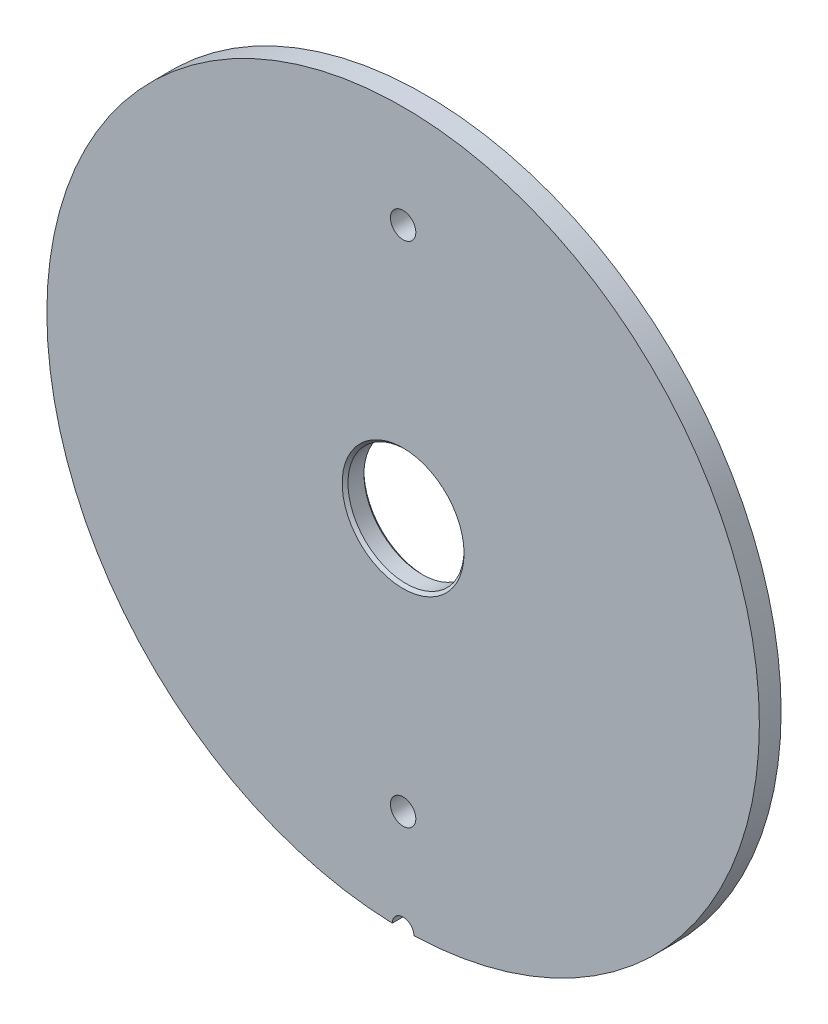
SolidWorks part; units mm, degrees
material "Acier non allié"
ref_plane "Plan de face" through (0, 0, 0) normal (0, 0, 1) x (1, 0, 0)
ref_plane "Plan de dessus" through (0, 0, 0) normal (0, 1, 0) x (1, 0, 0)
ref_plane "Plan de droite" through (0, 0, 0) normal (1, 0, 0) x (0, 0, -1)
sketch "Esquisse1" plane through (0, 0, 0) normal (0, 0, 1) x (1, 0, 0)
  circle A0 centre (0, 0) radius 245.5
  circle A1 centre (0, 0) radius 40
  dimension "D1" = 491
  dimension "D2" = 80
extrude "Boss.-Extru.1" add sketch "Esquisse1" along normal blind 15
hole_wizard "Dégagement M20" positions "Esquisse2" profile "Esquisse3" hole size "M12" standard "ISO" end condition up to next
sketch "Esquisse2" plane through (0, 0, 15) normal (0, 0, 1) x (1, 0, 0)
  line L0 (0, 0) -> (0, 266.4874) construction
  line L1 (0, 266.4874) -> (0, -277.0763) construction
  circle A0 centre (0, 0) radius 175
  point P0 (0, 175)
  point P2 (0, -175)
  dimension "D1" = 350
sketch "Esquisse3" plane through (0, 175, 15) normal (1, 0, 0) x (0, -1, 0)
  line L0 (0, 0) -> (0, 15)
  line L1 (0, 15) -> (8.75, 15)
  line L2 (8.75, 15) -> (8.75, 0)
  line L5 (8.75, 0) -> (0, 0)
  line L11 (0, -6.35) -> (0, 107.95) construction
  dimension "Diamètre du perçage jusqu'au prochain" = 17.5
  dimension "Profondeur du perçage jusqu'au prochain" = 15
chamfer "Chanfrein1" distance 2 angle 45 2 edges at (40, 0, 0) (40, 0, 15)
sketch "Esquisse4" plane through (0, 0, 0) normal (0, 0, -1) x (-1, 0, 0)
  circle A0 centre (0, -245.5) radius 7.5
  circle A1 centre (0, 0) radius 245.5 construction
  dimension "D1" = 15
extrude "Enlèv. mat.-Extru.1" cut sketch "Esquisse4" against normal up to next
